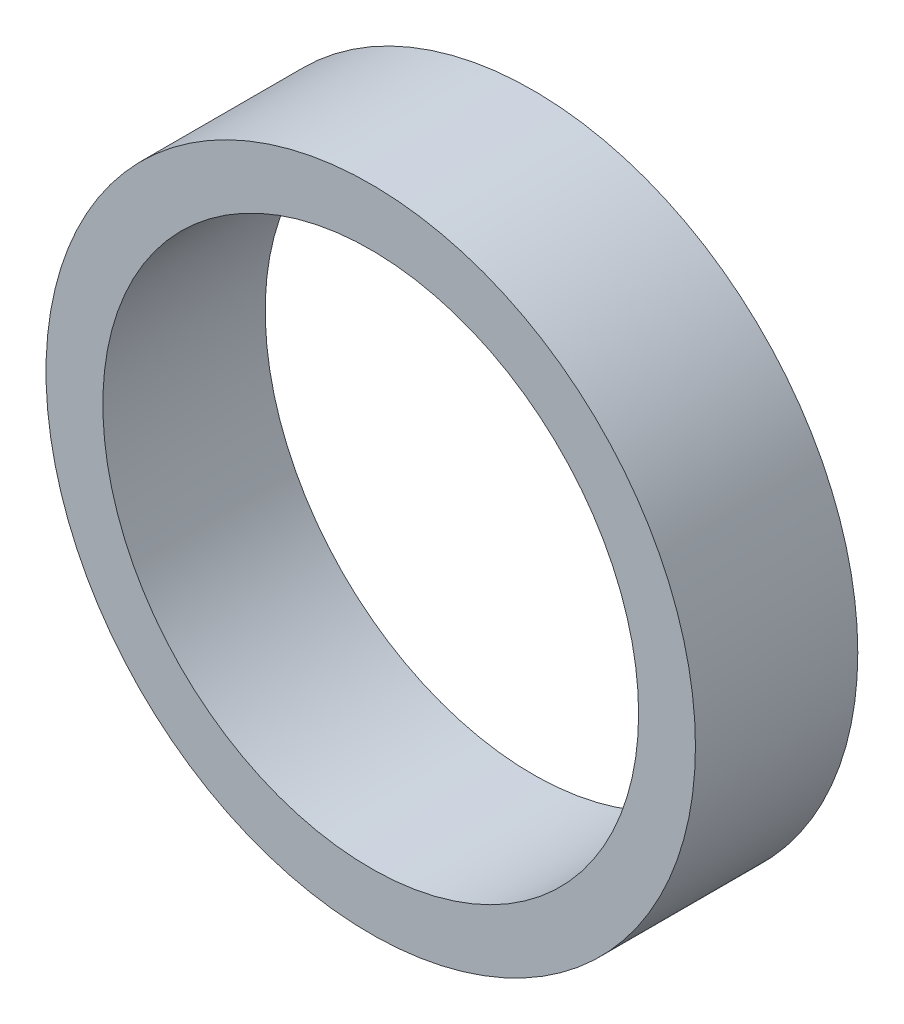
SolidWorks part; units mm, degrees
ref_plane "前视基准面" through (0, 0, 0) normal (0, 0, 1) x (1, 0, 0)
ref_plane "上视基准面" through (0, 0, 0) normal (0, 1, 0) x (1, 0, 0)
ref_plane "右视基准面" through (0, 0, 0) normal (1, 0, 0) x (0, 0, -1)
sketch "草图1" plane through (0, 0, 0) normal (0, 0, 1) x (1, 0, 0)
  circle A0 centre (0, 0) radius 40
  circle A1 centre (0, 0) radius 33 construction
  circle A2 centre (0, 0) radius 33
  dimension "D1" = 80
extrude "凸台-拉伸1" add sketch "草图1" against normal blind 20
